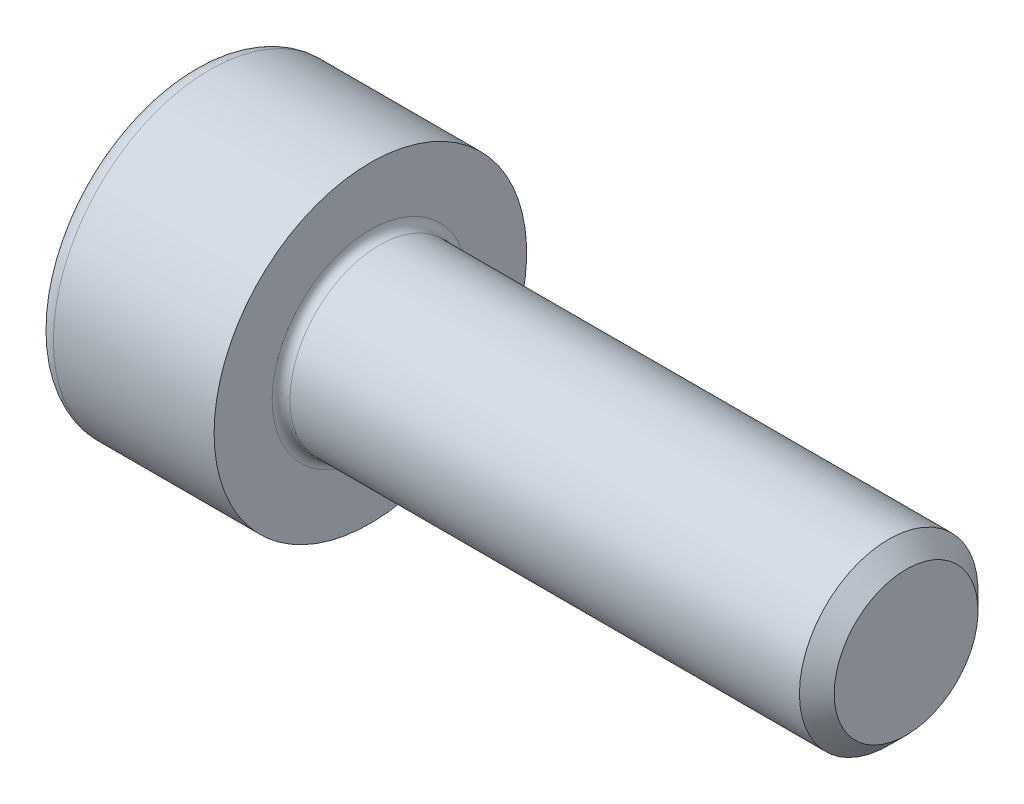
SolidWorks part; units mm, degrees
ref_plane "Plane1" through (0, 0, 0) normal (0, 0, 1) x (1, 0, 0)
ref_plane "Plane2" through (0, 0, 0) normal (0, 1, 0) x (1, 0, 0)
ref_plane "Plane3" through (0, 0, 0) normal (1, 0, 0) x (0, 0, -1)
sketch "BodySke" plane through (0, 0, 0) normal (0, 0, 1) x (1, 0, 0)
  line L0 (0, 0) -> (0, 3.5)
  line L1 (0, 3.5) -> (4, 3.5)
  line L2 (4, 3.5) -> (4, 2)
  line L3 (4, 2) -> (15.61, 2)
  line L4 (16, 1.61) -> (16, 0)
  line L5 (16, 0) -> (0, 0)
  line L6 (-31.75, 0) -> (127, 0) construction
  line L8 (16, 1.61) -> (15.61, 2)
  line L10 (16, -1.61) -> (15.61, -2) construction
  line L11 (4.7, 9.525) -> (4.7, 3.175) construction
  line L12 (4, 9.525) -> (4, 3.175) construction
  line L13 (-44, 9.525) -> (-44, 3.175) construction
  dimension "Diameter" = 4
  dimension "Head_ht" = 4
  dimension "Length" = 12
  dimension "Body_ch_ang" = 45
  dimension "Head_dia" = 7
  dimension "Minor_dia" = 3.22
  dimension "Advance" = 0.7
  dimension "Thread_nom" = 12
  dimension "Thread_length" = 60
revolve "Base-Revolve" add sketch "BodySke"
cosmetic thread "ThreadCosmetic"
fillet "Fillet1" radius 0.2 1 edges at (4, 0, 2)
fillet "Fillet2" radius 0.4 1 edges at (0, 0, 3.5)
sketch "Sketch2" plane through (0, 0, 0) normal (0, 0, 1) x (1, 0, 0)
  line L0 (0, 1.51) -> (2, 1.51)
  line L1 (2, 1.51) -> (2.8718, 0)
  line L2 (-31.75, 0) -> (127, 0) construction
  line L3 (2.8718, 0) -> (0, 0)
  line L4 (0, 0) -> (0, 1.51)
  line L6 (0, 0) -> (47.625, 0) construction
  dimension "D1" = 1.51
  dimension "D2" = 60
  dimension "Depth" = 2
revolve "Hex-PreBroach" cut sketch "Sketch2" angle 360 about L6
sketch "Sketch3" plane through (0, 0, 0) normal (-1, 0, 0) x (0, 0.5, 0.866)
  line L0 (0.8718, 1.51) -> (-0.8718, 1.51)
  line L1 (-0.8718, 1.51) -> (-1.7436, 0)
  line L2 (0.8718, 1.51) -> (1.7436, 0)
  line L3 (0.8718, -1.51) -> (1.7436, 0)
  line L4 (0.8718, -1.51) -> (-0.8718, -1.51)
  line L5 (-0.8718, -1.51) -> (-1.7436, 0)
  dimension "D1" = 1.51
  dimension "D2" = 1.51
  dimension "Hex_size" = 3.02
extrude "Hex" cut sketch "Sketch3" against normal blind 2
sketch "ThdSchSke" plane through (0, 0, 0) normal (0, 0, 1) x (1, 0, 0)
  line L0 (6.1, -1.61) -> (5.8269, -2)
  line L1 (6.1, -1.61) -> (6.3731, -2)
  line L2 (6.3731, -2) -> (6.3731, -2.5)
  line L3 (-3.175, 0) -> (5.1513, 0) construction
  line L4 (0, 3.1) -> (0, -3.1) construction
  line L5 (6.3731, -2.5) -> (5.8269, -2.5)
  line L6 (5.8269, -2.5) -> (5.8269, -2)
  dimension "Thread_minor" = 3.22
  dimension "Diameter" = 4
  dimension "Start" = 6.1
  dimension "SideAngle" = 55
  dimension "VeeAngle" = 70
  dimension "Overcut" = 5
revolve "ThreadSchematic" [suppressed] cut sketch "ThdSchSke" angle 360 about L3
pattern_linear "ThdSchPat" [suppressed]
equation "\"D2@Sketch3\" = \"Hex_size@Sketch3\" / 2"
equation "\"D1@Sketch3\" = \"Hex_size@Sketch3\" / 2"
equation "\"D1@Sketch2\" = \"Hex_size@Sketch3\" / 2"
equation "\"Thread_minor@ThreadCosmetic\"  =  \"Minor_dia@BodySke\""
equation "\"Depth@Sketch2\" =  \"Key_eng@Hex\""
equation "\"Thread_length@ThreadCosmetic\" = ((sgn( (\"Length@BodySke\" - \"Advance@BodySke\" * 3.0) - \"Thread_nom@BodySke\" )-1)*( (\"Length@BodySke\" - \"Advance@BodySke\" * 3.0) - \"Thread_nom@BodySke\" ))/-2+ \"Thread_nom@BodySke\""
equation "\"Thread_minor@ThdSchSke\" = \"Minor_dia@BodySke\""
equation "\"Diameter@ThdSchSke\" = \"Diameter@BodySke\""
equation "\"Overcut@ThdSchSke\" = \"Diameter@BodySke\" * 1.25"
equation "\"Start@ThdSchSke\" = \"Head_ht@BodySke\" + \"Length@BodySke\" - \"Thread_length@ThreadCosmetic\"  '---Non-countersunk---"
equation "\"Num_threads@ThdSchPat\" = int( \"Thread_length@ThreadCosmetic\" / \"Advance@BodySke\" + 0.999 )  + 1"
equation "\"Advance@ThdSchPat\" = \"Thread_length@ThreadCosmetic\" /  (\"Num_threads@ThdSchPat\" - 1) 'relax it"
equation "\"Num_threads@ThdSchPat\" = \"Num_threads@ThdSchPat\" - sgn( \"Num_threads@ThdSchPat\" - 1) '---chamfered tips only---"
